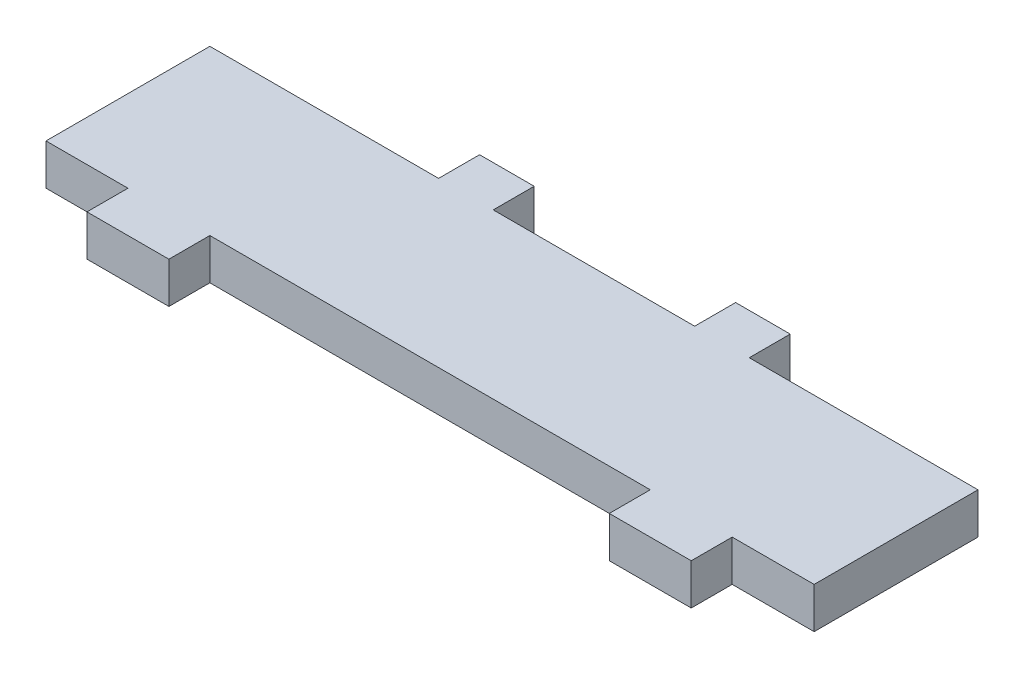
SolidWorks part; units mm, degrees
ref_plane "Front Plane" through (0, 0, 0) normal (0, 0, 1) x (1, 0, 0)
ref_plane "Top Plane" through (0, 0, 0) normal (0, 1, 0) x (1, 0, 0)
ref_plane "Right Plane" through (0, 0, 0) normal (1, 0, 0) x (0, 0, -1)
sketch "Sketch1" plane through (0, 0, 0) normal (0, 1, 0) x (1, 0, 0)
  line L1 (-56.25, -12) -> (56.25, -12)
  line L2 (-56.25, -12) -> (-56.25, 12)
  line L3 (-56.25, 12) -> (56.25, 12)
  line L4 (56.25, -12) -> (56.25, 12)
  line L5 (-56.25, -12) -> (56.25, 12) construction
  line L6 (-56.25, 12) -> (56.25, -12) construction
  point P0 (0, 0)
  dimension "D1" = 112.5
  dimension "D2" = 24
extrude "Boss-Extrude1" add sketch "Sketch1" along normal blind 6
sketch "Sketch2" plane through (0, 0, -12) normal (0, 0, -1) x (-1, 0, 0)
  line L0 (-56.25, 0) -> (56.25, 0) construction
  line L1 (22.75, 0) -> (14.75, 0)
  line L2 (22.75, 0) -> (22.75, 6)
  line L3 (22.75, 6) -> (14.75, 6)
  line L4 (14.75, 0) -> (14.75, 6)
  line L5 (-56.25, 6) -> (56.25, 6) construction
  line L6 (-14.75, 0) -> (-14.75, 6) construction
  line L7 (-14.75, 6) -> (-22.75, 6)
  line L8 (-14.75, 6) -> (-14.75, 0)
  line L9 (-14.75, 0) -> (-22.75, 0)
  line L10 (-22.75, 6) -> (-22.75, 0)
  line L11 (-22.75, 0) -> (-22.75, 6) construction
  line L12 (14.75, 0) -> (-14.75, 0)
  point P24 (0, 0)
  line M7 (-56.25, 0) -> (56.25, 0)
  line M9 (56.25, 6) -> (-56.25, 6)
extrude "Boss-Extrude2" add sketch "Sketch2" along normal blind 6 contours L10 L8 M9 M7 | L4 L2 M7 M9
sketch "Sketch3" plane through (0, 0, 12) normal (0, 0, 1) x (1, 0, 0)
  line L0 (-32.25, 0) -> (32.25, 0)
  line L1 (-56.25, 0) -> (56.25, 0) construction
  line L2 (32.25, 0) -> (32.25, 6) construction
  line L3 (-56.25, 6) -> (56.25, 6) construction
  line L4 (32.25, 0) -> (44.25, 0)
  line L5 (32.25, 0) -> (32.25, 6)
  line L6 (32.25, 6) -> (44.25, 6)
  line L7 (44.25, 0) -> (44.25, 6)
  line L8 (44.25, 0) -> (44.25, 6) construction
  line L10 (-32.25, 0) -> (-44.25, 0)
  line L11 (-32.25, 0) -> (-32.25, 6)
  line L12 (-32.25, 6) -> (-44.25, 6)
  line L13 (-44.25, 0) -> (-44.25, 6)
  point P7 (0, 0)
  line M6 (-56.25, 0) -> (56.25, 0)
  line M8 (56.25, 6) -> (-56.25, 6)
extrude "Boss-Extrude3" add sketch "Sketch3" along normal blind 6 contours L13 L11 M6 M8 | L7 L5 M6 M8
